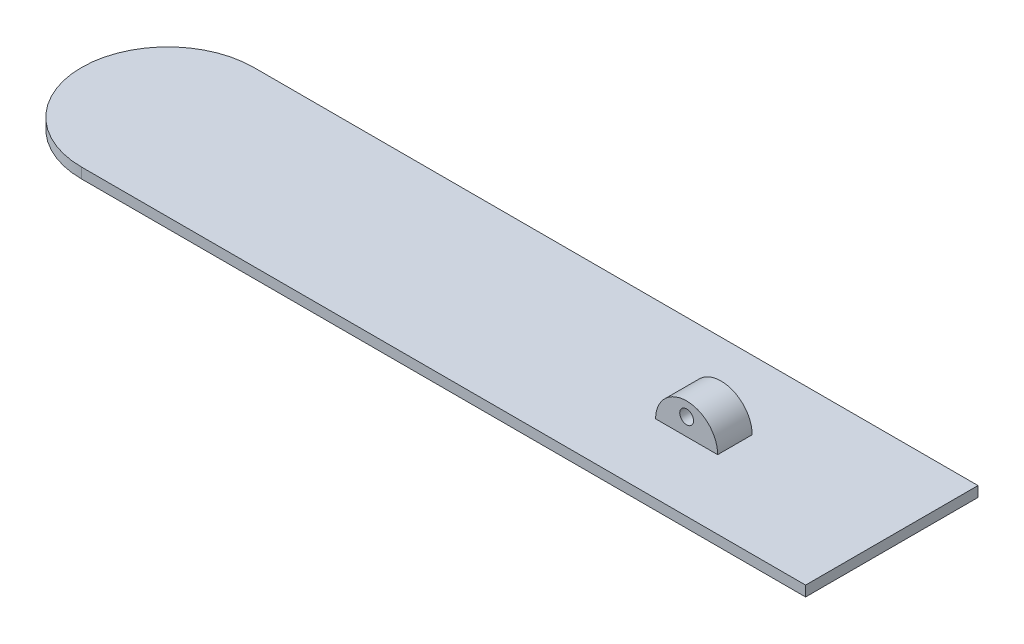
SolidWorks part; units mm, degrees
ref_plane "Front Plane" through (0, 0, 0) normal (0, 0, 1) x (1, 0, 0)
ref_plane "Top Plane" through (0, 0, 0) normal (0, 1, 0) x (1, 0, 0)
ref_plane "Right Plane" through (0, 0, 0) normal (1, 0, 0) x (0, 0, -1)
sketch "Sketch1" plane through (0, 0, 0) normal (0, 1, 0) x (1, 0, 0)
  line L1 (0, 0) -> (210, 0)
  line L2 (0, 0) -> (0, 50) construction
  line L3 (0, 50) -> (210, 50)
  line L4 (210, 0) -> (210, 50)
  line L5 (0, 0) -> (210, 50) construction
  line L6 (0, 50) -> (210, 0) construction
  arc A0 (0, 50) -> (0, 0) centre (0, 25) ccw
  point P4 (105, 25)
  dimension "D1" = 210
  dimension "D2" = 50
extrude "Boss-Extrude1" add sketch "Sketch1" along normal blind 3 contours L3 L4 L1 A0
sketch "Sketch2" plane through (0, 3, 0) normal (0, 1, 0) x (1, 0, 0)
  line L0 (0, 0) -> (210, 0) construction
  line L1 (0, 48) -> (52, 48) construction
  line L2 (0, 48) -> (0, 22) construction
  line L3 (0, 22) -> (52, 22) construction
  line L4 (52, 48) -> (52, 22) construction
  line L5 (0, 48) -> (52, 22) construction
  line L6 (0, 22) -> (52, 48) construction
  line L7 (2, 0) -> (16, 0) construction
  line L8 (2, 0) -> (2, 21) construction
  line L9 (2, 21) -> (16, 21) construction
  line L10 (16, 0) -> (16, 21) construction
  line L11 (2, 0) -> (16, 21) construction
  line L12 (2, 21) -> (16, 0) construction
  line L13 (19, 0) -> (33, 0) construction
  line L14 (19, 0) -> (19, 21) construction
  line L15 (19, 21) -> (33, 21) construction
  line L16 (33, 0) -> (33, 21) construction
  line L17 (36, 0) -> (50, 0) construction
  line L18 (36, 0) -> (36, 21) construction
  line L19 (36, 21) -> (50, 21) construction
  line L20 (50, 0) -> (50, 21) construction
  line L21 (0, 50) -> (210, 50) construction
  line L22 (206, 39) -> (194, 39) construction
  line L23 (-24.8193, 28) -> (-10.8193, 28) construction
  line L24 (-24.8193, 28) -> (-24.8193, 22) construction
  line L25 (-24.8193, 22) -> (-10.8193, 22) construction
  line L26 (-10.8193, 28) -> (-10.8193, 22) construction
  line L27 (-24.8193, 28) -> (-10.8193, 22) construction
  line L28 (-24.8193, 22) -> (-10.8193, 28) construction
  line L29 (56, 48) -> (136, 48) construction
  line L30 (56, 48) -> (56, 2) construction
  line L31 (56, 2) -> (136, 2) construction
  line L32 (136, 48) -> (136, 2) construction
  line L33 (56, 48) -> (136, 2) construction
  line L34 (56, 2) -> (136, 48) construction
  line L35 (194, 39) -> (194, 12) construction
  line L36 (194, 12) -> (198.5, 12) construction
  line L37 (198.5, 12) -> (198.5, 2) construction
  line L38 (198.5, 2) -> (201.5, 2) construction
  line L39 (201.5, 2) -> (201.5, 12) construction
  line L40 (201.5, 12) -> (206, 12) construction
  line L41 (206, 12) -> (206, 39) construction
  line L42 (210, 0) -> (210, 50) construction
  arc A0 (0, 50) -> (0, 0) centre (0, 25) ccw construction
  point P4 (26, 35)
  point P11 (9, 10.5)
  point P21 (26, 21)
  point P22 (26, 22)
  point P29 (-17.8193, 25)
  point P38 (96, 25)
  point P40 (200, 2)
  point P47 (200, 39)
  dimension "D1" = 26
  dimension "D2" = 52
  dimension "D3" = 14
  dimension "D4" = 21
  dimension "D5" = 14
  dimension "D6" = 14
  dimension "D7" = 2
  dimension "D8" = 2
  dimension "D9" = 2
  dimension "D10" = 6
  dimension "D11" = 14
  dimension "D12" = 46
  dimension "D13" = 80
  dimension "D14" = 2
  dimension "D15" = 4
  dimension "D16" = 27
  dimension "D17" = 10
  dimension "D18" = 12
  dimension "D19" = 3
  dimension "D20" = 4
ref_plane "Plane1" through (0, 0, -25) normal (0, 0, 1) x (1, 0, 0)
sketch "Sketch3" plane through (0, 0, -25) normal (0, 0, 1) x (1, 0, 0)
  line L0 (0, 3) -> (210, 3) construction
  line L1 (146.5, 3) -> (164.5, 3)
  arc A0 (164.5, 3) -> (146.5, 3) centre (155.5, 3) ccw
  circle A1 centre (155.5, 8) radius 2
  dimension "D1" = 4
  dimension "D2" = 5
  dimension "D3" = 9
  dimension "D4" = 45.5
extrude "Boss-Extrude2" add sketch "Sketch3" along normal mid plane 10
